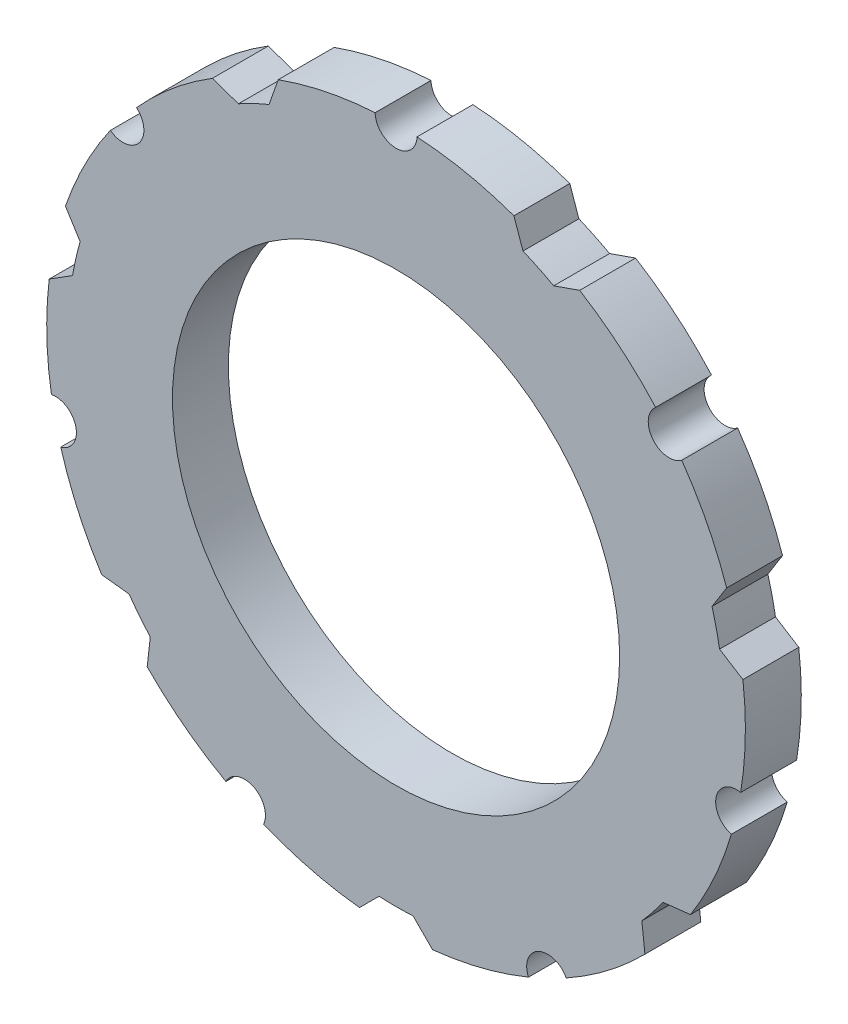
SolidWorks part; units mm, degrees
ref_plane "Front Plane" through (0, 0, 0) normal (0, 0, 1) x (1, 0, 0)
ref_plane "Top Plane" through (0, 0, 0) normal (0, 1, 0) x (1, 0, 0)
ref_plane "Right Plane" through (0, 0, 0) normal (1, 0, 0) x (0, 0, -1)
sketch "Sketch1" plane through (0, 0, 0) normal (0, 0, 1) x (1, 0, 0)
  line L0 (23.6582, 8.0801) -> (22.6089, 6.4101)
  line L1 (8.4334, 23.5346) -> (9.0848, 21.6729)
  line L2 (24.8212, 2.985) -> (23.1511, 4.0344)
  line L3 (13.142, 21.2671) -> (11.2803, 20.6157)
  line L4 (21.0679, -13.4589) -> (19.108, -13.6797)
  line L5 (17.8095, -17.5448) -> (17.5887, -15.5849)
  line L6 (2.6131, -24.8631) -> (1.2184, -23.4684)
  line L7 (-2.6131, -24.8631) -> (-1.2184, -23.4684)
  line L8 (-17.8095, -17.5448) -> (-17.5887, -15.5849)
  line L9 (-21.0679, -13.4589) -> (-19.108, -13.6797)
  line L10 (-24.8212, 2.985) -> (-23.1511, 4.0344)
  line L11 (-23.6582, 8.0801) -> (-22.6089, 6.4101)
  line L12 (-13.142, 21.2671) -> (-11.2803, 20.6157)
  line L13 (-8.4334, 23.5346) -> (-9.0848, 21.6729)
  circle A0 centre (0, 0) radius 16
  arc A1 (11.2803, 20.6157) -> (9.0848, 21.6729) centre (0, 0) ccw
  arc A2 (-1.4993, 24.955) -> (-8.4334, 23.5346) centre (0, 0) ccw
  arc A3 (-1.4993, 24.955) -> (1.4993, 24.955) centre (0, 25) ccw
  arc A4 (18.5758, 16.7314) -> (20.4454, 14.387) centre (19.5458, 15.5872) ccw
  arc A5 (24.663, -4.0913) -> (23.9957, -7.0147) centre (24.3732, -5.563) ccw
  arc A6 (12.1784, -21.8331) -> (9.4767, -23.1342) centre (10.8471, -22.5242) ccw
  arc A7 (-9.4767, -23.1342) -> (-12.1784, -21.8331) centre (-10.8471, -22.5242) ccw
  arc A8 (-23.9957, -7.0147) -> (-24.663, -4.0913) centre (-24.3732, -5.563) ccw
  arc A9 (-20.4454, 14.387) -> (-18.5758, 16.7314) centre (-19.5458, 15.5872) ccw
  arc A10 (18.5758, 16.7314) -> (13.142, 21.2671) centre (0, 0) ccw
  arc A11 (24.663, -4.0913) -> (24.8212, 2.985) centre (0, 0) ccw
  arc A12 (12.1784, -21.8331) -> (17.8095, -17.5448) centre (0, 0) ccw
  arc A13 (-9.4767, -23.1342) -> (-2.6131, -24.8631) centre (0, 0) ccw
  arc A14 (-23.9957, -7.0147) -> (-21.0679, -13.4589) centre (0, 0) ccw
  arc A15 (-20.4454, 14.387) -> (-23.6582, 8.0801) centre (0, 0) ccw
  arc A16 (8.4334, 23.5346) -> (1.4993, 24.955) centre (0, 0) ccw
  arc A17 (-9.0848, 21.6729) -> (-11.2803, 20.6157) centre (0, 0) ccw
  arc A18 (-22.6089, 6.4101) -> (-23.1511, 4.0344) centre (0, 0) ccw
  arc A19 (-19.108, -13.6797) -> (-17.5887, -15.5849) centre (0, 0) ccw
  arc A20 (-1.2184, -23.4684) -> (1.2184, -23.4684) centre (0, 0) ccw
  arc A21 (17.5887, -15.5849) -> (19.108, -13.6797) centre (0, 0) ccw
  arc A22 (23.1511, 4.0344) -> (22.6089, 6.4101) centre (0, 0) ccw
  arc A23 (-13.142, 21.2671) -> (-18.5758, 16.7314) centre (0, 0) ccw
  arc A24 (-24.8212, 2.985) -> (-24.663, -4.0913) centre (0, 0) ccw
  arc A25 (23.6582, 8.0801) -> (20.4454, 14.387) centre (0, 0) ccw
  arc A26 (-17.8095, -17.5448) -> (-12.1784, -21.8331) centre (0, 0) ccw
  arc A27 (2.6131, -24.8631) -> (9.4767, -23.1342) centre (0, 0) ccw
  arc A28 (21.0679, -13.4589) -> (23.9957, -7.0147) centre (0, 0) ccw
  dimension "D1" = 32
  dimension "D2" = 47
  dimension "D3" = 50
  dimension "D4" = 7
  dimension "D5" = 7
extrude "Boss-Extrude1" add sketch "Sketch1" along normal blind 4
